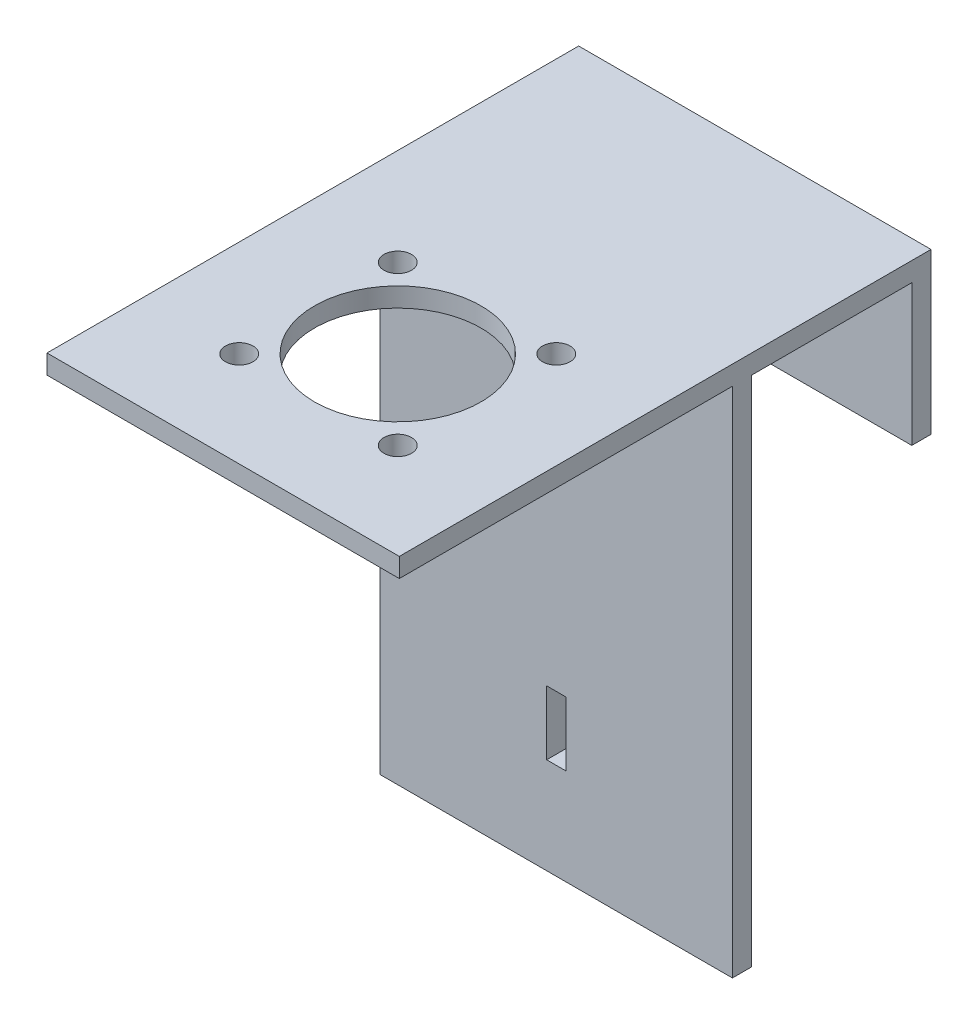
SolidWorks part; units mm, degrees
ref_plane "Front Plane" through (0, 0, 0) normal (0, 0, 1) x (1, 0, 0)
ref_plane "Top Plane" through (0, 0, 0) normal (0, 1, 0) x (1, 0, 0)
ref_plane "Right Plane" through (0, 0, 0) normal (1, 0, 0) x (0, 0, -1)
sketch "Sketch1" plane through (0, 0, 0) normal (0, 1, 0) x (1, 0, 0)
  line L0 (-27.5, 15) -> (27.5, 15) construction
  line L1 (-27.5, 40) -> (27.5, 40)
  line L2 (-27.5, 40) -> (-27.5, -40)
  line L3 (-27.5, -40) -> (27.5, -40)
  line L4 (27.5, 40) -> (27.5, -40)
  line L5 (0, -12.7439) -> (0, 4.7561) construction
  line L6 (0, 4.7561) -> (17.5, -12.7439) construction
  line L7 (17.5, -12.7439) -> (0, -12.7439) construction
  line L8 (0, -12.7439) -> (12.3744, -0.3696) construction
  circle A0 centre (0, -12.7439) radius 13
  circle A1 centre (0, -12.7439) radius 17.5 construction
  circle A2 centre (12.3744, -0.3696) radius 2.15
  circle A3 centre (12.3744, -25.1183) radius 2.15
  circle A4 centre (-12.3744, -25.1183) radius 2.15
  circle A5 centre (-12.3744, -0.3696) radius 2.15
  point P24 (0, -12.7439)
  dimension "D4" = 26
  dimension "D6" = 35
  dimension "D7" = 4.3
  dimension "D1" = 55
  dimension "D2" = 80
  dimension "D3" = 25
  dimension "D9" = 10.2439
  dimension "D5" = 4.5
  dimension "D8" = 4
extrude "Boss-Extrude2" add sketch "Sketch1" along normal blind 3
sketch "Sketch2" plane through (0, 0, 0) normal (0, -1, 0) x (1, 0, 0)
  line L0 (-27.5, -15) -> (27.5, -15) construction
  line L1 (-27.5, -40) -> (-27.5, 40) construction
  line L2 (27.5, 40) -> (27.5, -40) construction
  line L3 (27.5, -40) -> (-27.5, -40) construction
  line L4 (27.5, 40) -> (27.5, -40) construction
  line L5 (-27.5, -15) -> (27.5, -15)
  line L6 (-27.5, -15) -> (-27.5, -12)
  line L7 (-27.5, -12) -> (27.5, -12)
  line L8 (27.5, -15) -> (27.5, -12)
  dimension "D1" = 25
  dimension "D2" = 3
  dimension "D3" = 55
extrude "Boss-Extrude3" add sketch "Sketch2" along normal blind 80
sketch "Sketch3" plane through (0, 0, -15) normal (0, 0, -1) x (-1, 0, 0)
  line L0 (27.5, -60) -> (-27.5, -60) construction
  line L1 (27.5, -80) -> (27.5, 0) construction
  line L2 (-27.5, -80) -> (-27.5, 0) construction
  line L3 (27.5, 0) -> (-27.5, 0) construction
  line L4 (0, -60) -> (0, 0) construction
  line L5 (0, 0) -> (0, -80) construction
  line L6 (27.5, -80) -> (-27.5, -80) construction
  line L7 (-1.5, -55) -> (1.5, -65) construction
  line L8 (-1.5, -55) -> (1.5, -55)
  line L9 (-1.5, -55) -> (-1.5, -65)
  line L10 (-1.5, -65) -> (1.5, -65)
  line L11 (1.5, -55) -> (1.5, -65)
  dimension "D1" = 60
  dimension "D2" = 10
  dimension "D3" = 3
extrude "Cut-Extrude1" cut sketch "Sketch3" against normal blind 80
sketch "Sketch4" plane through (0, 0, -40) normal (0, 0, -1) x (-1, 0, 0)
  line L1 (-27.5, 3) -> (27.5, 3)
  line L2 (-27.5, 3) -> (-27.5, -22)
  line L3 (-27.5, -22) -> (27.5, -22)
  line L4 (27.5, 3) -> (27.5, -22)
  dimension "D1" = 55
  dimension "D2" = 25
extrude "Boss-Extrude4" add sketch "Sketch4" along normal blind 3
